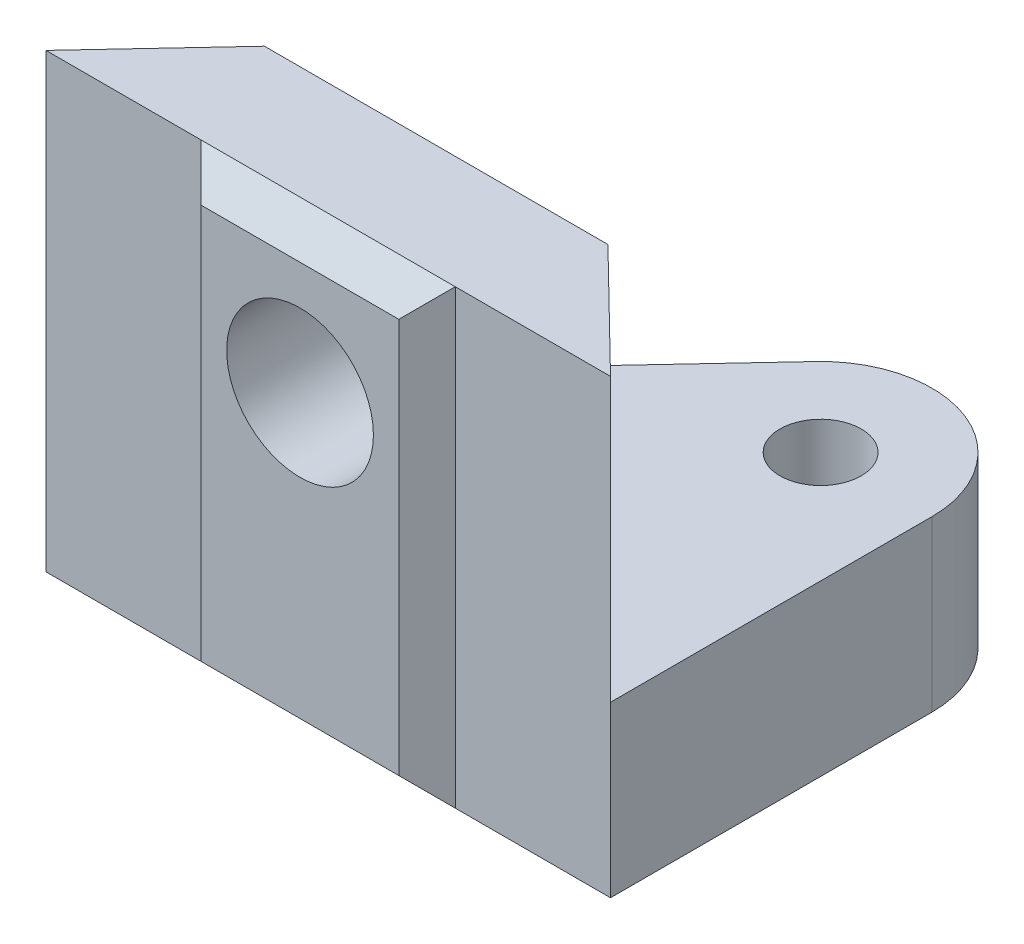
SolidWorks part; units mm, degrees
ref_plane "Front Plane" through (0, 0, 0) normal (0, 0, 1) x (1, 0, 0)
ref_plane "Top Plane" through (0, 0, 0) normal (0, 1, 0) x (1, 0, 0)
ref_plane "Right Plane" through (0, 0, 0) normal (1, 0, 0) x (0, 0, -1)
sketch "Sketch1" plane through (0, 0, 0) normal (0, 1, 0) x (1, 0, 0)
  line L0 (-6.5423, -4.7379) -> (13.4577, -4.7379)
  line L1 (13.4577, -4.7379) -> (9.3661, -0.7379)
  line L2 (9.3661, -0.7379) -> (-2.8009, -0.7379)
  line L3 (-2.8009, -0.7379) -> (-6.5423, -4.7379)
  dimension "D1" = 20
  dimension "D2" = 12.167
  dimension "D3" = 5.477
  dimension "D4" = 5.722
extrude "Boss-Extrude1" add sketch "Sketch1" against normal blind 16
sketch "Sketch2" plane through (0, 0, 4.7379) normal (0, 0, 1) x (1, 0, 0)
  line L0 (-1.0423, 0) -> (-1.0423, -16)
  line L1 (-6.5423, 0) -> (13.4577, 0) construction
  line L2 (-6.5423, -16) -> (13.4577, -16) construction
  line L3 (-1.0423, -16) -> (7.9577, -16)
  line L4 (7.9577, -16) -> (7.9577, 0)
  line L5 (7.9577, 0) -> (-1.0423, 0)
  line L6 (-6.5423, -16) -> (-6.5423, 0) construction
  line L7 (13.4577, -16) -> (13.4577, 0) construction
  dimension "D1" = 5.5
  dimension "D2" = 5.5
extrude "Boss-Extrude2" add sketch "Sketch2" along normal blind 1 draft 45
sketch "Sketch3" plane through (0, 0, 5.7379) normal (0, 0, 1) x (1, 0, 0)
  line L0 (3.4577, -1) -> (3.4577, -10.1599) construction
  line L2 (6.9577, -1) -> (-0.0423, -1) construction
  circle A0 centre (3.4577, -5) radius 2.6
  point P6 (0, 0)
  point P7 (0, 0)
  point P8 (3.4577, -7.0095)
  dimension "D1" = 5.2
  dimension "D2" = 4
extrude "Cut-Extrude1" cut sketch "Sketch3" against normal through all
sketch "Sketch4" plane through (0, -16, 0) normal (0, -1, 0) x (1, 0, 0)
  line L0 (-6.5423, 4.7379) -> (-6.5423, -10.5951) construction
  line L1 (-6.5423, -10.5951) -> (13.4577, -10.5951) construction
  line L2 (13.4577, -10.5951) -> (13.4577, 4.7379) construction
  line L3 (-6.5423, -6.6501) -> (13.4577, -6.6501) construction
  line L4 (-6.5423, 4.7379) -> (-1.0423, 4.7379) construction
  line L8 (13.4577, 4.7379) -> (13.4577, -6.6501)
  line L9 (-6.5423, 4.7379) -> (6.6318, -9.3451)
  line L10 (13.4577, 4.7379) -> (-6.5423, 4.7379)
  arc A0 (6.6318, -9.3451) -> (13.4577, -6.6501) centre (9.5127, -6.6501) ccw
  circle A1 centre (9.5127, -6.6501) radius 1.44
  dimension "D5" = 7.89
  dimension "D3" = 2.88
  dimension "D1" = 15.333
  dimension "D2" = 11.388
extrude "Boss-Extrude3" add sketch "Sketch4" against normal blind 6
